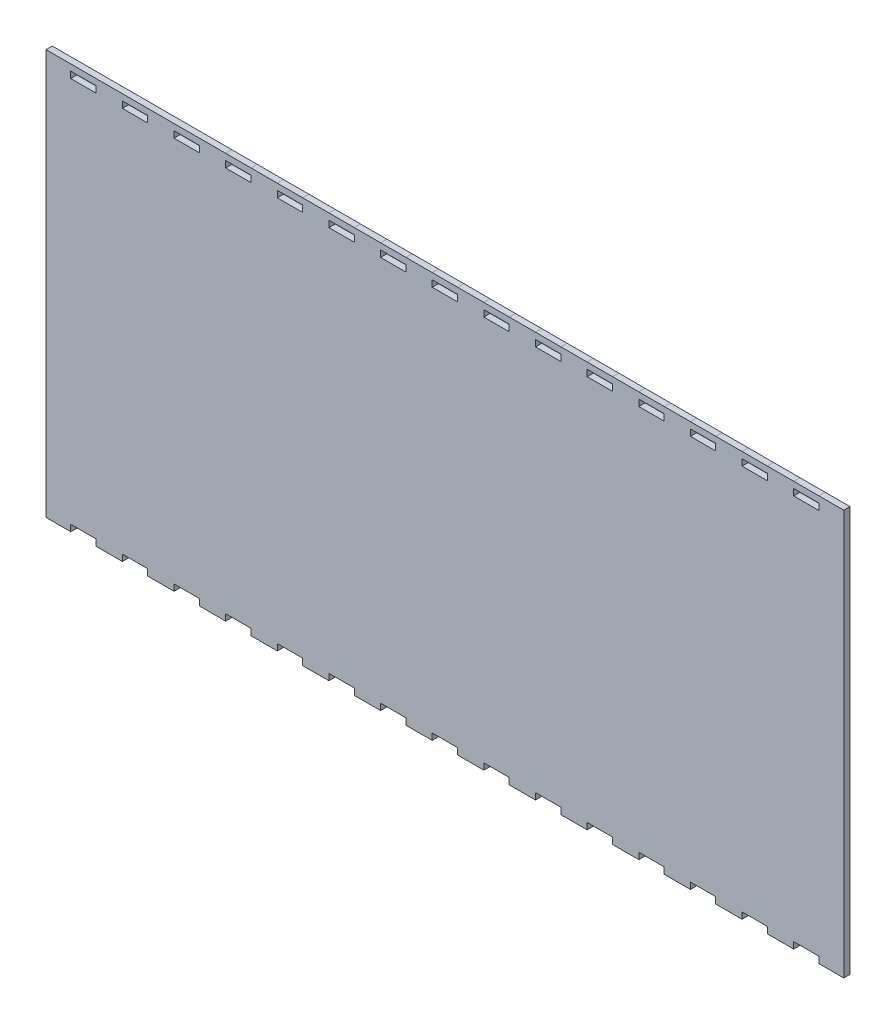
SolidWorks part; units mm, degrees
ref_plane "Front Plane" through (0, 0, 0) normal (0, 0, 1) x (1, 0, 0)
ref_plane "Top Plane" through (0, 0, 0) normal (0, 1, 0) x (1, 0, 0)
ref_plane "Right Plane" through (0, 0, 0) normal (1, 0, 0) x (0, 0, -1)
sketch "Sketch1" plane through (0, 0, 0) normal (0, 0, 1) x (1, 0, 0)
  line L248 (393.8, 203.2) -> (393.8, 199.925)
  line L249 (393.8, 199.925) -> (380.9, 199.925)
  line L250 (380.9, 199.925) -> (380.9, 203.2)
  line L251 (380.9, 203.2) -> (367.4929, 203.2)
  line L252 (367.4929, 203.2) -> (367.4929, 199.925)
  line L253 (367.4929, 199.925) -> (354.5929, 199.925)
  line L254 (354.5929, 199.925) -> (354.5929, 203.2)
  line L255 (354.5929, 203.2) -> (341.1857, 203.2)
  line L256 (341.1857, 203.2) -> (341.1857, 199.925)
  line L257 (341.1857, 199.925) -> (328.2857, 199.925)
  line L258 (328.2857, 199.925) -> (328.2857, 203.2)
  line L259 (328.2857, 203.2) -> (314.8786, 203.2)
  line L260 (314.8786, 203.2) -> (314.8786, 199.925)
  line L261 (314.8786, 199.925) -> (301.9786, 199.925)
  line L262 (301.9786, 199.925) -> (301.9786, 203.2)
  line L263 (301.9786, 203.2) -> (288.5714, 203.2)
  line L264 (288.5714, 203.2) -> (288.5714, 199.925)
  line L265 (288.5714, 199.925) -> (275.6714, 199.925)
  line L266 (275.6714, 199.925) -> (275.6714, 203.2)
  line L267 (275.6714, 203.2) -> (262.2643, 203.2)
  line L268 (262.2643, 203.2) -> (262.2643, 199.925)
  line L269 (262.2643, 199.925) -> (249.3643, 199.925)
  line L270 (249.3643, 199.925) -> (249.3643, 203.2)
  line L271 (249.3643, 203.2) -> (235.9571, 203.2)
  line L272 (235.9571, 203.2) -> (235.9571, 199.925)
  line L273 (235.9571, 199.925) -> (223.0571, 199.925)
  line L274 (223.0571, 199.925) -> (223.0571, 203.2)
  line L275 (223.0571, 203.2) -> (209.65, 203.2)
  line L276 (209.65, 203.2) -> (209.65, 199.925)
  line L277 (209.65, 199.925) -> (196.75, 199.925)
  line L278 (196.75, 199.925) -> (196.75, 203.2)
  line L279 (196.75, 203.2) -> (183.3429, 203.2)
  line L280 (183.3429, 203.2) -> (183.3429, 199.925)
  line L281 (183.3429, 199.925) -> (170.4429, 199.925)
  line L282 (170.4429, 199.925) -> (170.4429, 203.2)
  line L283 (170.4429, 203.2) -> (157.0357, 203.2)
  line L284 (157.0357, 203.2) -> (157.0357, 199.925)
  line L285 (157.0357, 199.925) -> (144.1357, 199.925)
  line L286 (144.1357, 199.925) -> (144.1357, 203.2)
  line L287 (144.1357, 203.2) -> (130.7286, 203.2)
  line L288 (130.7286, 203.2) -> (130.7286, 199.925)
  line L289 (130.7286, 199.925) -> (117.8286, 199.925)
  line L290 (117.8286, 199.925) -> (117.8286, 203.2)
  line L291 (117.8286, 203.2) -> (104.4214, 203.2)
  line L292 (104.4214, 203.2) -> (104.4214, 199.925)
  line L293 (104.4214, 199.925) -> (91.5214, 199.925)
  line L294 (91.5214, 199.925) -> (91.5214, 203.2)
  line L295 (91.5214, 203.2) -> (78.1143, 203.2)
  line L296 (78.1143, 203.2) -> (78.1143, 199.925)
  line L297 (78.1143, 199.925) -> (65.2143, 199.925)
  line L298 (65.2143, 199.925) -> (65.2143, 203.2)
  line L299 (65.2143, 203.2) -> (51.8071, 203.2)
  line L300 (51.8071, 203.2) -> (51.8071, 199.925)
  line L301 (51.8071, 199.925) -> (38.9071, 199.925)
  line L302 (38.9071, 199.925) -> (38.9071, 203.2)
  line L303 (38.9071, 203.2) -> (25.5, 203.2)
  line L304 (25.5, 203.2) -> (25.5, 199.925)
  line L305 (25.5, 199.925) -> (12.6, 199.925)
  line L306 (12.6, 199.925) -> (12.6, 203.2254)
  line L307 (12.6, 203.2254) -> (0, 203.2254)
  line L308 (0, 203.2254) -> (0, -0.0254)
  line L309 (0, -0.0254) -> (12.6, -0.0254)
  line L310 (12.6, -0.0254) -> (12.6, 3.275)
  line L311 (12.6, 3.275) -> (25.5, 3.275)
  line L312 (25.5, 3.275) -> (25.5, 0)
  line L313 (25.5, 0) -> (38.9071, 0)
  line L314 (38.9071, 0) -> (38.9071, 3.275)
  line L315 (38.9071, 3.275) -> (51.8071, 3.275)
  line L316 (51.8071, 3.275) -> (51.8071, 0)
  line L317 (51.8071, 0) -> (65.2143, 0)
  line L318 (65.2143, 0) -> (65.2143, 3.275)
  line L319 (65.2143, 3.275) -> (78.1143, 3.275)
  line L320 (78.1143, 3.275) -> (78.1143, 0)
  line L321 (78.1143, 0) -> (91.5214, 0)
  line L322 (91.5214, 0) -> (91.5214, 3.275)
  line L323 (91.5214, 3.275) -> (104.4214, 3.275)
  line L324 (104.4214, 3.275) -> (104.4214, 0)
  line L325 (104.4214, 0) -> (117.8286, 0)
  line L326 (117.8286, 0) -> (117.8286, 3.275)
  line L327 (117.8286, 3.275) -> (130.7286, 3.275)
  line L328 (130.7286, 3.275) -> (130.7286, 0)
  line L329 (130.7286, 0) -> (144.1357, 0)
  line L330 (144.1357, 0) -> (144.1357, 3.275)
  line L331 (144.1357, 3.275) -> (157.0357, 3.275)
  line L332 (157.0357, 3.275) -> (157.0357, 0)
  line L333 (157.0357, 0) -> (170.4429, 0)
  line L334 (170.4429, 0) -> (170.4429, 3.275)
  line L335 (170.4429, 3.275) -> (183.3429, 3.275)
  line L336 (183.3429, 3.275) -> (183.3429, 0)
  line L337 (183.3429, 0) -> (196.75, 0)
  line L338 (196.75, 0) -> (196.75, 3.275)
  line L339 (196.75, 3.275) -> (209.65, 3.275)
  line L340 (209.65, 3.275) -> (209.65, 0)
  line L341 (209.65, 0) -> (223.0571, 0)
  line L342 (223.0571, 0) -> (223.0571, 3.275)
  line L343 (223.0571, 3.275) -> (235.9571, 3.275)
  line L344 (235.9571, 3.275) -> (235.9571, 0)
  line L345 (235.9571, 0) -> (249.3643, 0)
  line L346 (249.3643, 0) -> (249.3643, 3.275)
  line L347 (249.3643, 3.275) -> (262.2643, 3.275)
  line L348 (262.2643, 3.275) -> (262.2643, 0)
  line L349 (262.2643, 0) -> (275.6714, 0)
  line L350 (275.6714, 0) -> (275.6714, 3.275)
  line L351 (275.6714, 3.275) -> (288.5714, 3.275)
  line L352 (288.5714, 3.275) -> (288.5714, 0)
  line L353 (288.5714, 0) -> (301.9786, 0)
  line L354 (301.9786, 0) -> (301.9786, 3.275)
  line L355 (301.9786, 3.275) -> (314.8786, 3.275)
  line L356 (314.8786, 3.275) -> (314.8786, 0)
  line L357 (314.8786, 0) -> (328.2857, 0)
  line L358 (328.2857, 0) -> (328.2857, 3.275)
  line L359 (328.2857, 3.275) -> (341.1857, 3.275)
  line L360 (341.1857, 3.275) -> (341.1857, 0)
  line L361 (341.1857, 0) -> (354.5929, 0)
  line L362 (354.5929, 0) -> (354.5929, 3.275)
  line L363 (354.5929, 3.275) -> (367.4929, 3.275)
  line L364 (367.4929, 3.275) -> (367.4929, 0)
  line L365 (367.4929, 0) -> (380.9, 0)
  line L366 (380.9, 0) -> (380.9, 3.275)
  line L367 (380.9, 3.275) -> (393.8, 3.275)
  line L368 (393.8, 3.275) -> (393.8, 0)
  line L369 (393.8, 0) -> (406.4, 0)
  line L370 (406.4, 0) -> (406.4, 203.2)
  line L371 (406.4, 203.2) -> (393.8, 203.2)
extrude "Boss-Extrude1" add sketch "Sketch1" along normal blind 3.175
sketch "Sketch2" plane through (0, 203.2254, 0) normal (0, 1, 0) x (1, 0, 0)
  line L0 (406.4, 0) -> (393.8, 0) construction
  line L1 (393.8, 0) -> (393.8, -3.175) construction
  line L2 (393.8, -3.175) -> (406.4, -3.175) construction
  line L3 (406.4, -3.175) -> (406.4, 0) construction
  line L4 (12.6, 0) -> (0, 0)
  line L5 (0, 0) -> (0, -3.175)
  line L6 (0, -3.175) -> (12.6, -3.175)
  line L7 (12.6, -3.175) -> (12.6, 0)
  line L8 (12.6, 0) -> (0, 0)
  line L9 (0, 0) -> (0, -3.175)
  line L10 (0, -3.175) -> (12.6, -3.175)
  line L11 (12.6, -3.175) -> (12.6, 0)
  line L12 (380.9, 0) -> (367.4929, 0) construction
  line L13 (367.4929, 0) -> (367.4929, -3.175) construction
  line L14 (367.4929, -3.175) -> (380.9, -3.175) construction
  line L15 (380.9, -3.175) -> (380.9, 0) construction
  line L16 (354.5929, 0) -> (341.1857, 0) construction
  line L17 (341.1857, 0) -> (341.1857, -3.175) construction
  line L18 (341.1857, -3.175) -> (354.5929, -3.175) construction
  line L19 (354.5929, -3.175) -> (354.5929, 0) construction
  line L20 (328.2857, 0) -> (314.8786, 0) construction
  line L21 (314.8786, 0) -> (314.8786, -3.175) construction
  line L22 (314.8786, -3.175) -> (328.2857, -3.175) construction
  line L23 (328.2857, -3.175) -> (328.2857, 0) construction
  line L24 (301.9786, 0) -> (288.5714, 0) construction
  line L25 (288.5714, 0) -> (288.5714, -3.175) construction
  line L26 (288.5714, -3.175) -> (301.9786, -3.175) construction
  line L27 (301.9786, -3.175) -> (301.9786, 0) construction
  line L28 (275.6714, 0) -> (262.2643, 0) construction
  line L29 (262.2643, 0) -> (262.2643, -3.175) construction
  line L30 (262.2643, -3.175) -> (275.6714, -3.175) construction
  line L31 (275.6714, -3.175) -> (275.6714, 0) construction
  line L32 (249.3643, 0) -> (235.9571, 0) construction
  line L33 (235.9571, 0) -> (235.9571, -3.175) construction
  line L34 (235.9571, -3.175) -> (249.3643, -3.175) construction
  line L35 (249.3643, -3.175) -> (249.3643, 0) construction
  line L36 (223.0571, 0) -> (209.65, 0) construction
  line L37 (209.65, 0) -> (209.65, -3.175) construction
  line L38 (209.65, -3.175) -> (223.0571, -3.175) construction
  line L39 (223.0571, -3.175) -> (223.0571, 0) construction
  line L40 (196.75, 0) -> (183.3429, 0) construction
  line L41 (183.3429, 0) -> (183.3429, -3.175) construction
  line L42 (183.3429, -3.175) -> (196.75, -3.175) construction
  line L43 (196.75, -3.175) -> (196.75, 0) construction
  line L44 (170.4429, 0) -> (157.0357, 0) construction
  line L45 (157.0357, 0) -> (157.0357, -3.175) construction
  line L46 (157.0357, -3.175) -> (170.4429, -3.175) construction
  line L47 (170.4429, -3.175) -> (170.4429, 0) construction
  line L48 (144.1357, 0) -> (130.7286, 0) construction
  line L49 (130.7286, 0) -> (130.7286, -3.175) construction
  line L50 (130.7286, -3.175) -> (144.1357, -3.175) construction
  line L51 (144.1357, -3.175) -> (144.1357, 0) construction
  line L52 (117.8286, 0) -> (104.4214, 0) construction
  line L53 (104.4214, 0) -> (104.4214, -3.175) construction
  line L54 (104.4214, -3.175) -> (117.8286, -3.175) construction
  line L55 (117.8286, -3.175) -> (117.8286, 0) construction
  line L56 (65.2143, 0) -> (51.8071, 0) construction
  line L57 (51.8071, 0) -> (51.8071, -3.175) construction
  line L58 (51.8071, -3.175) -> (65.2143, -3.175) construction
  line L59 (65.2143, -3.175) -> (65.2143, 0) construction
  line L60 (91.5214, 0) -> (78.1143, 0) construction
  line L61 (78.1143, 0) -> (78.1143, -3.175) construction
  line L62 (78.1143, -3.175) -> (91.5214, -3.175) construction
  line L63 (91.5214, -3.175) -> (91.5214, 0) construction
  line L64 (38.9071, 0) -> (25.5, 0) construction
  line L65 (25.5, 0) -> (25.5, -3.175) construction
  line L66 (25.5, -3.175) -> (38.9071, -3.175) construction
  line L67 (38.9071, -3.175) -> (38.9071, 0) construction
  line L68 (275.6714, -3.175) -> (262.2643, -3.175) construction
  line L69 (117.8286, -3.175) -> (104.4214, -3.175) construction
  line L70 (406.4, 0) -> (393.8, 0)
  line L71 (393.8, 0) -> (393.8, -3.175)
  line L72 (393.8, -3.175) -> (406.4, -3.175)
  line L73 (406.4, -3.175) -> (406.4, 0)
  line L74 (380.9, 0) -> (367.4929, 0)
  line L75 (367.4929, 0) -> (367.4929, -3.175)
  line L76 (367.4929, -3.175) -> (380.9, -3.175)
  line L77 (380.9, -3.175) -> (380.9, 0)
  line L78 (354.5929, 0) -> (341.1857, 0)
  line L79 (341.1857, 0) -> (341.1857, -3.175)
  line L80 (341.1857, -3.175) -> (354.5929, -3.175)
  line L81 (354.5929, -3.175) -> (354.5929, 0)
  line L82 (328.2857, 0) -> (314.8786, 0)
  line L83 (314.8786, 0) -> (314.8786, -3.175)
  line L84 (314.8786, -3.175) -> (328.2857, -3.175)
  line L85 (328.2857, -3.175) -> (328.2857, 0)
  line L86 (301.9786, 0) -> (288.5714, 0)
  line L87 (288.5714, 0) -> (288.5714, -3.175)
  line L88 (288.5714, -3.175) -> (301.9786, -3.175)
  line L89 (301.9786, -3.175) -> (301.9786, 0)
  line L90 (275.6714, 0) -> (262.2643, 0)
  line L91 (262.2643, 0) -> (262.2643, -3.175)
  line L92 (262.2643, -3.175) -> (275.6714, -3.175)
  line L93 (275.6714, -3.175) -> (275.6714, 0)
  line L94 (249.3643, 0) -> (235.9571, 0)
  line L95 (235.9571, 0) -> (235.9571, -3.175)
  line L96 (235.9571, -3.175) -> (249.3643, -3.175)
  line L97 (249.3643, -3.175) -> (249.3643, 0)
  line L98 (223.0571, 0) -> (209.65, 0)
  line L99 (209.65, 0) -> (209.65, -3.175)
  line L100 (209.65, -3.175) -> (223.0571, -3.175)
  line L101 (223.0571, -3.175) -> (223.0571, 0)
  line L102 (196.75, 0) -> (183.3429, 0)
  line L103 (183.3429, 0) -> (183.3429, -3.175)
  line L104 (183.3429, -3.175) -> (196.75, -3.175)
  line L105 (196.75, -3.175) -> (196.75, 0)
  line L106 (170.4429, 0) -> (157.0357, 0)
  line L107 (157.0357, 0) -> (157.0357, -3.175)
  line L108 (157.0357, -3.175) -> (170.4429, -3.175)
  line L109 (170.4429, -3.175) -> (170.4429, 0)
  line L110 (144.1357, 0) -> (130.7286, 0)
  line L111 (130.7286, 0) -> (130.7286, -3.175)
  line L112 (130.7286, -3.175) -> (144.1357, -3.175)
  line L113 (144.1357, -3.175) -> (144.1357, 0)
  line L114 (117.8286, 0) -> (104.4214, 0)
  line L115 (104.4214, 0) -> (104.4214, -3.175)
  line L116 (104.4214, -3.175) -> (117.8286, -3.175)
  line L117 (117.8286, -3.175) -> (117.8286, 0)
  line L118 (65.2143, 0) -> (51.8071, 0)
  line L119 (51.8071, 0) -> (51.8071, -3.175)
  line L120 (51.8071, -3.175) -> (65.2143, -3.175)
  line L121 (65.2143, -3.175) -> (65.2143, 0)
  line L122 (91.5214, 0) -> (78.1143, 0)
  line L123 (78.1143, 0) -> (78.1143, -3.175)
  line L124 (78.1143, -3.175) -> (91.5214, -3.175)
  line L125 (91.5214, -3.175) -> (91.5214, 0)
  line L126 (38.9071, 0) -> (25.5, 0)
  line L127 (25.5, 0) -> (25.5, -3.175)
  line L128 (25.5, -3.175) -> (38.9071, -3.175)
  line L129 (38.9071, -3.175) -> (38.9071, 0)
  line L130 (275.6714, -3.175) -> (262.2643, -3.175)
  line L131 (117.8286, -3.175) -> (104.4214, -3.175)
  dimension "D1" = 0
extrude "Boss-Extrude3" add sketch "Sketch2" along normal blind 3.175 and the other way blind 0.635 contours L128 L129 L126 L127 | L120 L121 L118 L119 | L112 L113 L110 L111 | L108 L109 L106 L107 | L100 L101 L98 L99 | L84 L85 L82 L83 | L8 L9 L10 L11 | L122 L123 L124 L125 | L116 L117 L114 L115 | L102 L103 L104 L105 | L94 L95 L96 L97 | L90 L91 L92 L93 | L86 L87 L88 L89 | L78 L79 L80 L81 | L74 L75 L76 L77 | L70 L71 L72 L73
sketch "Sketch3" plane through (12.6, 0, 0) normal (1, 0, 0) x (0, 0, -1)
  line L0 (0, 199.925) -> (0, 206.4004) construction
  line L1 (-3.175, 206.4004) -> (0, 206.4004)
  line L2 (-3.175, 206.4004) -> (-3.175, 203.2254)
  line L3 (-3.175, 203.2254) -> (0, 203.2254)
  line L4 (0, 206.4004) -> (0, 203.2254)
  dimension "D1" = 3.175
extrude "Boss-Extrude4" add sketch "Sketch3" along normal up to surface (381.2 mm away) up to face at (393.8, 203.1627, 1.5875)
